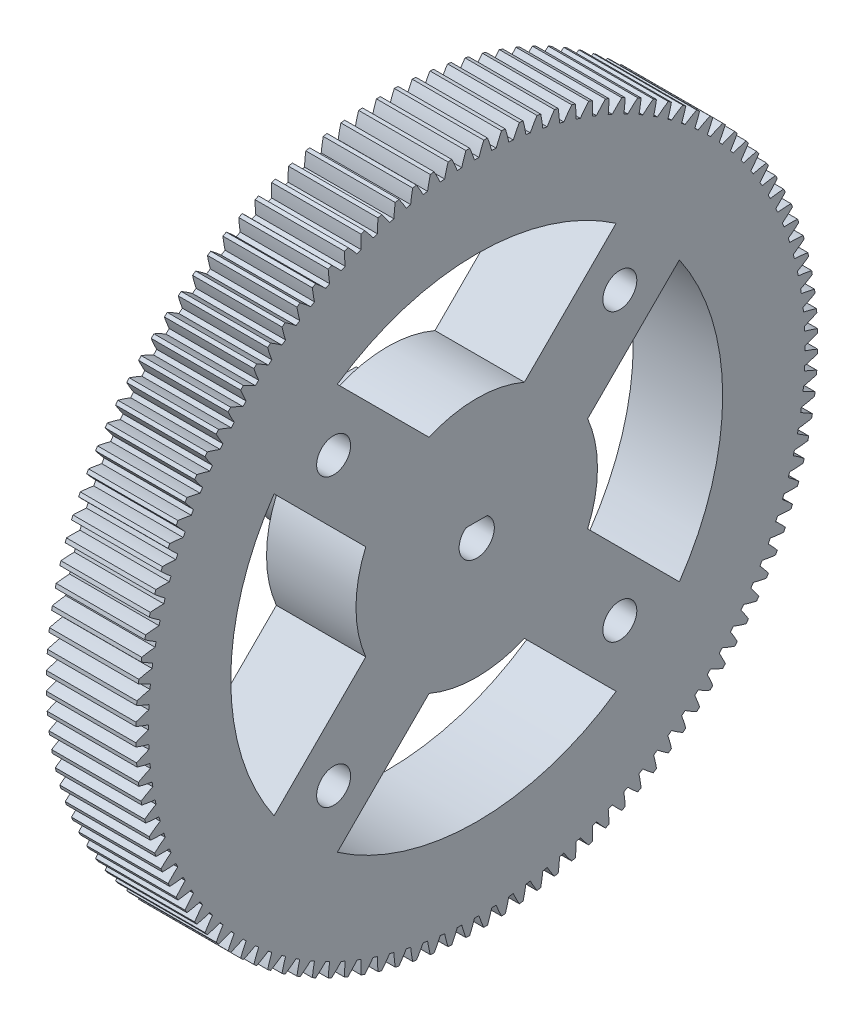
SolidWorks part; units mm, degrees
ref_plane "Plane1" through (0, 0, 0) normal (0, 0, 1) x (1, 0, 0)
ref_plane "Plane2" through (0, 0, 0) normal (0, 1, 0) x (1, 0, 0)
ref_plane "Plane3" through (0, 0, 0) normal (1, 0, 0) x (0, 0, -1)
sketch "HoldingSke" plane through (0, 0, 0) normal (0, 1, 0) x (1, 0, 0)
  line L0 (0, 0) -> (-406.4, -703.9054)
  line L1 (-15, 0) -> (100, 0) construction
  line L2 (0, 0) -> (-2.1039, 2.3779)
  line L3 (0, 0) -> (-11.863, 4.5341)
  line L4 (0, 0) -> (-4.318, 7.479)
  line L5 (0, 0) -> (-47.5972, -17.7524)
  line L6 (0, 0) -> (-10.5278, -7.1032)
  line L7 (-2.1039, 2.3779) -> (8.8308, 51.9871)
  line L8 (-76.2, 54.61) -> (-71.1708, 54.61)
  line L9 (-71.009, 38.7566) -> (-53.1078, 45.2721)
  line L10 (-76.2, 71.12) -> (104.1128, 71.12)
  line L11 (0, 0) -> (-12.7, 0)
  line L12 (-76.2, 101.6) -> (-76.1716, 101.6)
  line L13 (24.9733, 27.94) -> (52.9518, 28.4284)
  line L14 (24.9733, 27.94) -> (25.0241, 27.9398)
  line L15 (24.9733, 27.94) -> (100.4021, 29.52)
  circle A0 centre (0, 0) radius 2.3812
  circle A1 centre (0, 0) radius 38.1
  circle A2 centre (0, 0) radius 38.1
  circle A3 centre (0, 0) radius 2.3812
  dimension "MHD" = 76.2
  dimension "Hub_dia" = 76.2
  dimension "Bore" = 4.7625
  dimension "MBD" = 4.7625
  dimension "Num_teeth" = 120
  dimension "Pitch" = 812.8
  dimension "Overall_len" = 50.8
  dimension "Show_teeth" = 120
  dimension "Thickness" = 12.7
  dimension "OAL" = 50.8001
  dimension "T_dim" = 5.0292
  dimension "Ap" = 20
  dimension "H" = 19.05
  dimension "Pitch_radius" = 180.3128
  dimension "Width" = 12.7
  dimension "Backlash" = 0.0284
  dimension "Addendum_fac" = 1
  dimension "Dedendum_fac" = 1.2
  dimension "Clearance_fac" = 0.2
  dimension "Dedendum_add" = 0.0508
sketch "BasProSke" plane through (0, 0, 0) normal (0, 1, 0) x (1, 0, 0)
  line L0 (-10, 0) -> (60, 0) construction
  line L1 (0, 0) -> (0, 48.4187)
  line L2 (0, 0) -> (12.7, 0)
  line L3 (12.7, 0) -> (12.7, 48.4187)
  line L4 (12.7, 48.4187) -> (0, 48.4187)
  dimension "Thickness" = 12.7
  dimension "Diameter" = 96.8375
revolve "Base-Revolve" add sketch "BasProSke" angle 360 about L0
sketch "TooCutSke" plane through (0, 0, 0) normal (1, 0, 0) x (0, 0, -1)
  line L1 (0, 0) -> (0, 107) construction
  line L2 (0, 0) -> (-0.6732, 47.6202) construction
  line L3 (0, 0) -> (-2.4932, 95.2105) construction
  line L4 (-0.6732, 47.6202) -> (-1.2466, 47.6052) construction
  arc A0 (0.3197, 46.6206) -> (-0.3197, 46.6206) centre (0, 0) ccw
  arc A1 (1.0083, 48.4337) -> (-1.0083, 48.4337) centre (0, 0) ccw
  circle A2 centre (0, 0) radius 47.625 construction
  circle A3 centre (0, 0) radius 44.7529 construction
  arc A4 (-0.3197, 46.6206) -> (-1.0083, 48.4337) centre (-18.45, 40.7728) ccw
  arc A5 (1.0083, 48.4337) -> (0.3197, 46.6206) centre (18.45, 40.7728) ccw
  dimension "Root_dia" = 93.2434
  dimension "Overcut_dia" = 96.8883
  dimension "Pitch_dia" = 95.25
  dimension "Base_dia" = 89.5057
  dimension "Flank_rad" = 19.05
  dimension "Half_ang" = 1.5
  dimension "Half_CT" = 0.5736
extrude "ToothCut" cut sketch "TooCutSke" along normal through all
fillet "Breaks" [suppressed] radius 0.0159
fillet "RootFillets" [suppressed] radius 0.2095
pattern_circular "TeethCuts" count 120 every 3 about axis through (-10, 0, 0) along (1, 0, 0) of "ToothCut", "RootFillets", "Breaks"
sketch "HubNeaOneSke" plane through (0, 0, 0) normal (-1, 0, 0) x (0, 0, 1)
  circle A0 centre (0, 0) radius 38.1
  dimension "Diameter" = 76.2
extrude "HubNearOne" [suppressed] add sketch "HubNeaOneSke" along normal blind 38.1001
sketch "HubNeaBotSke" plane through (0, 0, 0) normal (-1, 0, 0) x (0, 0, 1)
  circle A0 centre (0, 0) radius 38.1
  dimension "Diameter" = 76.2
extrude "HubNearBoth" [suppressed] add sketch "HubNeaBotSke" along normal blind 19.05
ref_plane "FarPln" through (12.7, 0, 0) normal (1, 0, 0) x (0, 0, -1)
sketch "HubFarSke" plane through (12.7, 0, 0) normal (1, 0, 0) x (0, 0, -1)
  circle A0 centre (0, 0) radius 38.1
  dimension "Diameter" = 76.2
extrude "HubFar" [suppressed] add sketch "HubFarSke" along normal blind 19.05
sketch "BorSke" plane through (0, 0, 0) normal (1, 0, 0) x (0, 0, -1)
  circle A0 centre (0, 0) radius 2.3812
  dimension "Diameter" = 4.7625
extrude "Bore" cut sketch "BorSke" along normal mid plane 101.6001
sketch "KeySke" plane through (0, 0, 0) normal (1, 0, 0) x (0, 0, -1)
  line L0 (-0.127, 0) -> (-0.127, 2.6479)
  line L1 (-0.127, 2.6479) -> (0.127, 2.6479)
  line L2 (0.127, 2.6479) -> (0.127, 0)
  line L3 (0, 0) -> (0, 34) construction
  line L4 (-0.127, 0) -> (0.127, 0)
  dimension "Offset" = 2.648
  dimension "Width" = 0.254
extrude "Keyway" [suppressed] cut sketch "KeySke" along normal mid plane 101.6001
pattern_circular "Keyway2" [suppressed] count 2 every 90 about axis through (-10, 0, 0) along (1, 0, 0)
sketch "Sketch1" plane through (12.7, 0, 0) normal (1, 0, 0) x (0, 0, -1)
  line L0 (0, 25.6558) -> (0, -26.1333) construction
  line L1 (-24.8431, 0) -> (25.1424, 0) construction
  line L2 (-20.32, 20.32) -> (-20.32, -20.32) construction
  line L3 (-20.32, -20.32) -> (20.32, -20.32) construction
  line L4 (20.32, -20.32) -> (20.32, 20.32) construction
  line L5 (20.32, 20.32) -> (-20.32, 20.32) construction
  circle A0 centre (-20.32, 20.32) radius 2.413
  circle A1 centre (20.32, 20.32) radius 2.413
  circle A2 centre (20.32, -20.32) radius 2.413
  circle A3 centre (-20.32, -20.32) radius 2.413
  point P7 (0, 20.32)
  point P10 (20.32, 0)
  dimension "D3" = 4.826
  dimension "D1" = 40.64
  dimension "D2" = 40.64
extrude "Cut-Extrude1" cut sketch "Sketch1" against normal up to surface (12.7 mm away) up to face at (0, 0, -2.3812)
sketch "Sketch2" plane through (12.7, 0, 0) normal (1, 0, 0) x (0, 0, -1)
  circle A0 centre (0, 0) radius 5.461
  dimension "D1" = 10.922
extrude "Cut-Extrude2" cut sketch "Sketch2" against normal up to surface (12.7 mm away)
sketch "Sketch3" plane through (12.7, 0, 0) normal (1, 0, 0) x (0, 0, -1)
  line L0 (-20.32, -20.32) -> (20.32, 20.32) construction
  line L1 (-20.32, 20.32) -> (20.32, -20.32) construction
  line L2 (19.794, -28.7742) -> (6.7711, -15.7513)
  line L3 (28.7742, -19.794) -> (15.7513, -6.7711)
  line L4 (-28.7742, -19.794) -> (-15.7513, -6.7711)
  line L5 (-19.794, -28.7742) -> (-6.7711, -15.7513)
  line L6 (-6.7711, 15.7513) -> (-19.794, 28.7742)
  line L7 (6.7711, 15.7513) -> (19.794, 28.7742)
  line L8 (-15.7513, 6.7711) -> (-28.7742, 19.794)
  line L12 (15.7513, 6.7711) -> (28.7742, 19.794)
  arc A0 (-28.7742, 19.794) -> (-28.7742, -19.794) centre (0, 0) ccw
  arc A1 (-15.7513, 6.7711) -> (-15.7513, -6.7711) centre (0, 0) ccw
  arc A2 (-6.7711, -15.7513) -> (6.7711, -15.7513) centre (0, 0) ccw
  arc A3 (15.7513, -6.7711) -> (15.7513, 6.7711) centre (0, 0) ccw
  arc A4 (6.7711, 15.7513) -> (-6.7711, 15.7513) centre (0, 0) ccw
  arc A5 (19.794, 28.7742) -> (-19.794, 28.7742) centre (0, 0) ccw
  arc A6 (28.7742, -19.794) -> (28.7742, 19.794) centre (0, 0) ccw
  arc A7 (-19.794, -28.7742) -> (19.794, -28.7742) centre (0, 0) ccw
  dimension "D1" = 69.85
  dimension "D2" = 17.78
  dimension "D3" = 12.7
  dimension "D4" = 12.7
extrude "Cut-Extrude3" cut sketch "Sketch3" against normal up to surface (12.7 mm away)
sketch "Sketch4" plane through (12.7, 0, 0) normal (1, 0, 0) x (0, 0, -1)
  circle A0 centre (0, 0) radius 2.5019
  circle A1 centre (0, 0) radius 5.461
  circle A2 centre (0, 0) radius 5.461 construction
  dimension "D1" = 5.0038
extrude "Boss-Extrude1" add sketch "Sketch4" against normal up to surface (12.7 mm away)
sketch "Sketch5" plane through (12.7, 0, 0) normal (1, 0, 0) x (0, 0, -1)
  line L0 (-1.5112, 1.9939) -> (1.5112, 1.9939)
  line L1 (-1.6042, -2.5019) -> (1.6042, -2.5019) construction
  circle A0 centre (0, 0) radius 2.5019 construction
  arc A1 (-1.5112, 1.9939) -> (1.5112, 1.9939) centre (0, 0) cw
  point P6 (0, -2.5019)
  point P7 (0, 1.9939)
  dimension "D1" = 4.4958
extrude "Boss-Extrude2" add sketch "Sketch5" against normal up to surface (12.7 mm away)
sketch "Sketch6" plane through (0, 0, 0) normal (-1, 0, 0) x (0, 0, 1)
  line L0 (-5.7489, 6.731) -> (5.7489, 6.731)
  line L1 (-1.5112, 1.9939) -> (1.5112, 1.9939) construction
  circle A0 centre (0, 0) radius 2.5019
  arc A1 (-1.5112, 1.9939) -> (1.5112, 1.9939) centre (0, 0) ccw construction
  arc A2 (-5.7489, 6.731) -> (5.7489, 6.731) centre (0, 0) ccw
  point P11 (0, 1.9939)
  point P12 (0, 6.731)
  dimension "D1" = 6.35
  dimension "D2" = 6.731
extrude "Boss-Extrude3" add sketch "Sketch6" along normal blind 10.16
sketch "Sketch8" plane through (0, 6.731, 0) normal (0, 1, 0) x (1, 0, 0)
  line L0 (0, -5.7489) -> (0, 5.7489) construction
  circle A0 centre (-5.08, 0) radius 1.7526
  dimension "D1" = 3.5052
  dimension "D2" = 5.08
extrude "Cut-Extrude4" cut sketch "Sketch8" against normal up to surface (4.9455 mm away)
equation "' \"Pitch@HoldingSke\" = 4"
equation "' \"Num_teeth@HoldingSke\" = 12"
equation "' \"Ap@HoldingSke\" =  20"
equation "' \"Ap@HoldingSke\" = 20"
equation "' \"Width@HoldingSke\" = 0.5"
equation "' \"Hub_dia@HoldingSke\"= 1"
equation "' \"Hub_dia@HoldingSke\" = 1"
equation "' \"Overall_len@HoldingSke\" = 1.0"
equation "' \"Bore@HoldingSke\" = 0.75"
equation "' \"T_dim@HoldingSke\" = 0.85"
equation "' \"Width@KeySke\" = 0.25"
equation "' \"Show_teeth@HoldingSke\" = 13"
equation "' \"Backlash@HoldingSke\" = 0.009"
equation "' \"Addendum_fac@HoldingSke\" = 1.0"
equation "' \"Dedendum_fac@HoldingSke\" = 1.25"
equation "' \"Dedendum_add@HoldingSke\" = 0.00005"
equation "' \"Clearance_fac@HoldingSke\" = 0.25"
equation "' \"Pitch@HoldingSke\" = 0.5"
equation "' \"Num_teeth@HoldingSke\" = 23"
equation "' \"Show_teeth@HoldingSke\" = 23"
equation "' \"Backlash@HoldingSke\" = 0.0375"
equation "\"Overcut_dia@TooCutSke\" = (\"Num_teeth@HoldingSke\" + 2 * \"Addendum_fac@HoldingSke\") / \"Pitch@HoldingSke\" + 0.002"
equation "\"Pitch_dia@TooCutSke\" = \"Num_teeth@HoldingSke\" / \"Pitch@HoldingSke\""
equation "\"Base_dia@TooCutSke\" = \"Num_teeth@HoldingSke\" / \"Pitch@HoldingSke\" * cos((\"Ap@HoldingSke\"  * 3.14159265 / 180))"
equation "\"Root_dia@TooCutSke\" = (\"Num_teeth@HoldingSke\" + 2) / \"Pitch@HoldingSke\" - 2 * (\"Addendum_fac@HoldingSke\" + \"Dedendum_fac@HoldingSke\") / \"Pitch@HoldingSke\" - \"Dedendum_add@HoldingSke\" * 2"
equation "\"Half_ang@TooCutSke\" = 180 / \"Num_teeth@HoldingSke\""
equation "\"Half_CT@TooCutSke\" = \"Num_teeth@HoldingSke\" / \"Pitch@HoldingSke\" * sin((3.14159265 / 2 / \"Num_teeth@HoldingSke\")) / 2 - 7 * \"Backlash@HoldingSke\" / 4"
equation "\"Flank_rad@TooCutSke\" = \"Num_teeth@HoldingSke\" / \"Pitch@HoldingSke\" / 5"
equation "\"Radius@RootFillets\" = \"Clearance_fac@HoldingSke\" / \"Pitch@HoldingSke\" + \"Dedendum_add@HoldingSke\""
equation "\"Break_rad@Breaks\" = 0.02 / \"Pitch@HoldingSke\""
equation "\"Thickness@HoldingSke\" = \"Width@HoldingSke\""
equation "\"OAL@HoldingSke\" = \"Thickness@HoldingSke\""
equation "\"MHD@HoldingSke\" = (\"Num_teeth@HoldingSke\" + 2) / \"Pitch@HoldingSke\" - 2 * (\"Addendum_fac@HoldingSke\" + \"Dedendum_fac@HoldingSke\")  / \"Pitch@HoldingSke\" - \"Dedendum_add@HoldingSke\" * 2"
equation "\"MBD@HoldingSke\" = (\"Num_teeth@HoldingSke\" + 2) / \"Pitch@HoldingSke\" - 2 * (\"Addendum_fac@HoldingSke\" + \"Dedendum_fac@HoldingSke\")  / \"Pitch@HoldingSke\" - \"Dedendum_add@HoldingSke\" * 2 - 0.002"
equation "\"MHD@HoldingSke\" = ((sgn( \"MHD@HoldingSke\" - \"Hub_dia@HoldingSke\" )-1)*( \"MHD@HoldingSke\" - \"Hub_dia@HoldingSke\" ))/-2+ \"Hub_dia@HoldingSke\""
equation "\"MBD@HoldingSke\" = ((sgn( \"MBD@HoldingSke\" - \"Bore@HoldingSke\" )-1)*( \"MBD@HoldingSke\" - \"Bore@HoldingSke\" ))/-2+ \"Bore@HoldingSke\""
equation "\"OAL@HoldingSke\" = ((sgn( \"OAL@HoldingSke\" - \"Overall_len@HoldingSke\" )+1)*( \"OAL@HoldingSke\" - \"Overall_len@HoldingSke\" ))/2 + \"Overall_len@HoldingSke\" + 0.000002"
equation "\"Num_teeth@TeethCuts\" = int( \"Show_teeth@HoldingSke\" ) + 1"
equation "\"Num_teeth@TeethCuts\" = ((sgn( \"Num_teeth@TeethCuts\" - \"Num_teeth@HoldingSke\" )-1)*( \"Num_teeth@TeethCuts\" - \"Num_teeth@HoldingSke\" ))/-2+ \"Num_teeth@HoldingSke\""
equation "\"Num_teeth@TeethCuts\" = ((sgn( \"Num_teeth@TeethCuts\" - 2.0)+1)*( \"Num_teeth@TeethCuts\" - 2.0))/2 +2.0"
equation "\"Angle@TeethCuts\" = 360.0 / \"Num_teeth@HoldingSke\""
equation "\"Diameter@BasProSke\" = (\"Num_teeth@HoldingSke\" + 2 * \"Addendum_fac@HoldingSke\") / \"Pitch@HoldingSke\""
equation "\"Thickness@BasProSke\"  = \"Thickness@HoldingSke\""
equation "' \"Fillet_rad@BasProSke\" =  \"Thickness@HoldingSke\" * 0.05"
equation "' \"Fillet_rad@BasProSke\" = \"Thickness@HoldingSke\" * 0.05"
equation "\"MHD@HoldingSke\" = ((sgn( \"MHD@HoldingSke\" - \"Root_dia@TooCutSke\" )-1)*( \"MHD@HoldingSke\" - \"Root_dia@TooCutSke\" ))/-2+ \"Root_dia@TooCutSke\""
equation "\"Diameter@HubNeaOneSke\" = \"MHD@HoldingSke\""
equation "\"Length@HubNearOne\" = \"OAL@HoldingSke\" - \"Thickness@BasProSke\""
equation "\"Diameter@HubNeaBotSke\" = \"MHD@HoldingSke\""
equation "\"Length@HubNearBoth\" = ( \"OAL@HoldingSke\" - \"Thickness@BasProSke\" ) / 2.0"
equation "\"Thickness@FarPln\" = \"Thickness@BasProSke\""
equation "\"Diameter@HubFarSke\" = \"MHD@HoldingSke\""
equation "\"Length@HubFar\" = ( \"OAL@HoldingSke\" - \"Thickness@BasProSke\" ) / 2.0"
equation "\"Diameter@BorSke\" = \"MBD@HoldingSke\""
equation "\"D1@Bore\" = \"OAL@HoldingSke\" * 2.0"
equation "\"D1@Keyway\" = \"OAL@HoldingSke\" * 2.0"
equation "\"Offset@KeySke\" = \"T_dim@HoldingSke\" - \"MBD@HoldingSke\" / 2.0"
equation "\"o.5\"=0.672596"
